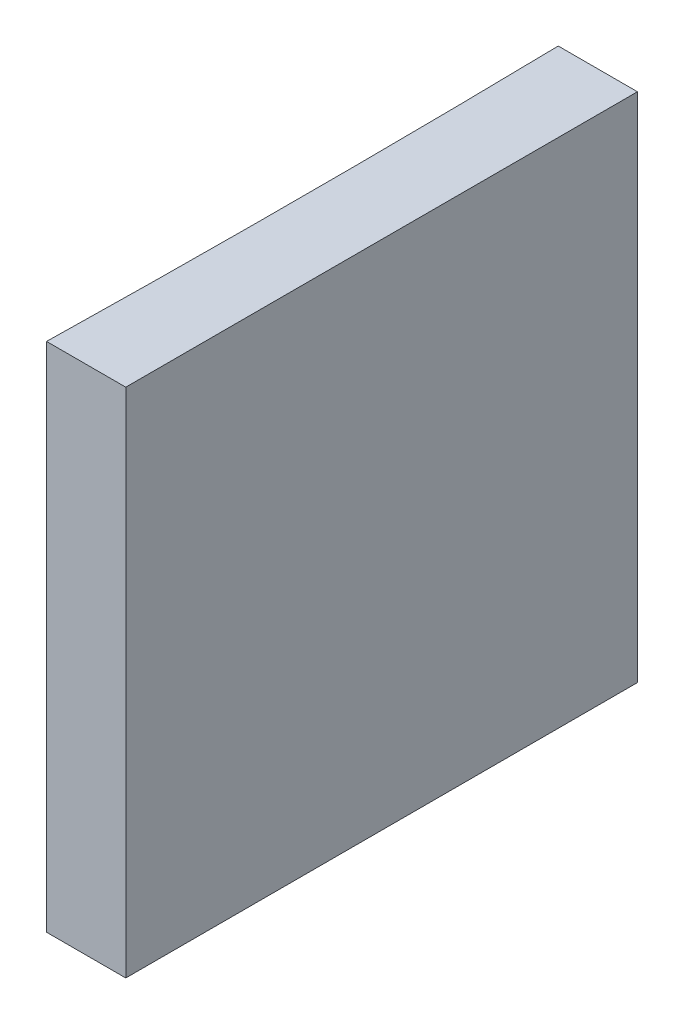
SolidWorks part; units mm, degrees
ref_plane "前视基准面" through (0, 0, 0) normal (0, 0, 1) x (1, 0, 0)
ref_plane "上视基准面" through (0, 0, 0) normal (0, 1, 0) x (1, 0, 0)
ref_plane "右视基准面" through (0, 0, 0) normal (1, 0, 0) x (0, 0, -1)
sketch "草图1" plane through (0, 0, 0) normal (0, 1, 0) x (1, 0, 0)
  line L0 (0, 0) -> (0, -20)
  line L1 (0, 0) -> (-3.0968, 0)
  line L2 (0, -20) -> (-3.0968, -20)
  line L3 (8.2336, -10) -> (-10.4405, -10) construction
  arc A0 (-3.0968, -20) -> (-3.0968, 0) centre (-519.8, -10) ccw
  point P7 (-3, -10)
  point P8 (0, -10)
  dimension "D2" = 516.8
  dimension "D3" = 3
  dimension "D1" = 20
extrude "凸台-拉伸1" add sketch "草图1" along normal blind 20
